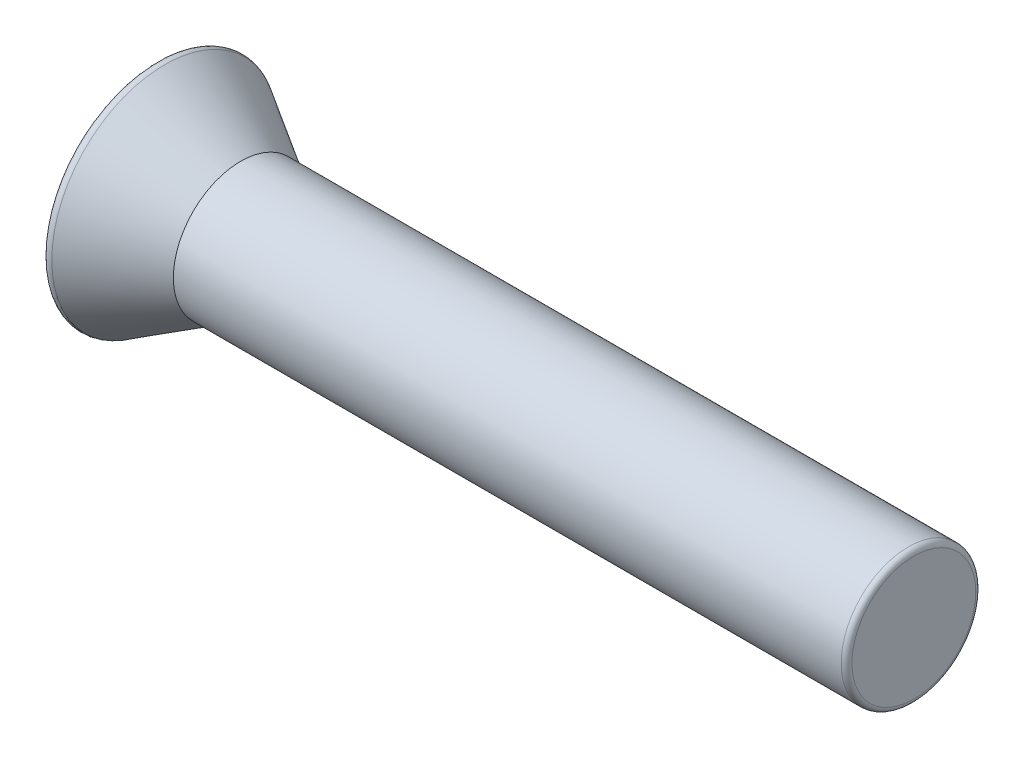
SolidWorks part; units mm, degrees
ref_plane "前视基准面" through (0, 0, 0) normal (0, 0, 1) x (1, 0, 0)
ref_plane "上视基准面" through (0, 0, 0) normal (0, 1, 0) x (1, 0, 0)
ref_plane "右视基准面" through (0, 0, 0) normal (1, 0, 0) x (0, 0, -1)
sketch "草图1" plane through (0, 0, 0) normal (0, 0, 1) x (1, 0, 0)
  line L0 (0, 0) -> (-6.816, 0) construction
  line L1 (0, 0) -> (0, 3.5)
  line L2 (0, 0) -> (2.5, 0)
  line L3 (2.5, 0) -> (2.5, 2)
  line L4 (0, 3.5) -> (2.5, 2)
revolve "旋转1" add sketch "草图1" angle 360 about L0
fillet "圆角1" radius 0.16 1 edges at (0, 0, -3.5)
sketch "草图2" plane through (2.5, 0, 0) normal (1, 0, 0) x (0, 0, -1)
  circle A0 centre (0, 0) radius 2
extrude "凸台-拉伸1" add sketch "草图2" along normal blind 20
fillet "圆角2" radius 0.16 1 edges at (22.5, 0, -2)
sketch "草图3" plane through (0, 0, 0) normal (-1, 0, 0) x (0, 0, 1)
  line L0 (0.41, -0.41) -> (0.41, -2.15)
  line L1 (-0.41, 2.15) -> (0.41, 2.15)
  line L2 (-0.41, 2.15) -> (-0.41, 0.41)
  line L3 (-0.41, -2.15) -> (0.41, -2.15)
  line L4 (0.41, 2.15) -> (0.41, 0.41)
  line L5 (0.41, -0.41) -> (2.15, -0.41)
  line L7 (-2.15, 0.41) -> (-0.41, 0.41)
  line L8 (-2.15, 0.41) -> (-2.15, -0.41)
  line L9 (-2.15, -0.41) -> (-0.41, -0.41)
  line L10 (2.15, 0.41) -> (2.15, -0.41)
  line L15 (-0.41, -0.41) -> (-0.41, -2.15)
  line L18 (0.41, 0.41) -> (2.15, 0.41)
  point P0 (0, 0)
  point P6 (0, 0)
extrude "切除-拉伸1" cut sketch "草图3" against normal blind 1
